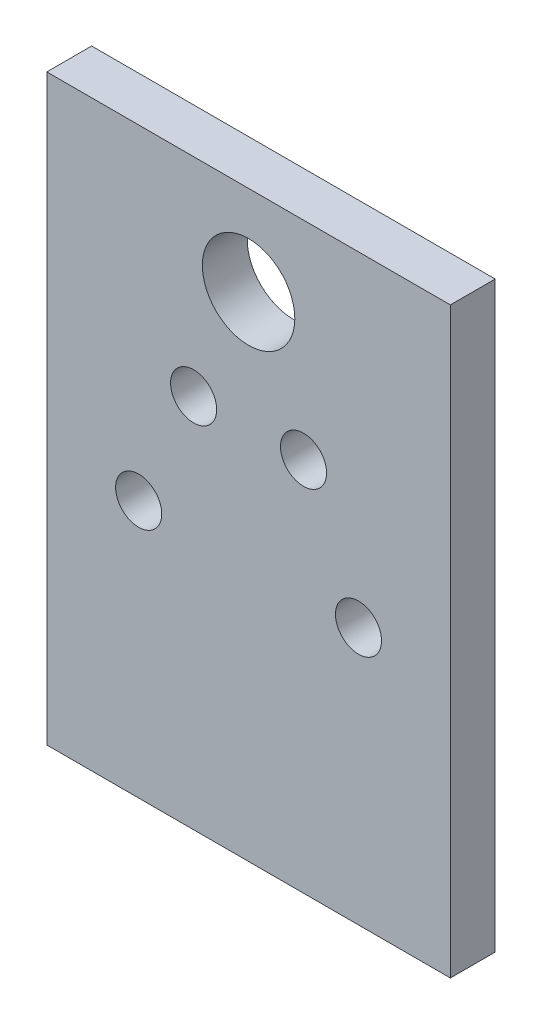
SolidWorks part; units mm, degrees
material "1060 Alloy"
ref_plane "Front Plane" through (0, 0, 0) normal (0, 0, 1) x (1, 0, 0)
ref_plane "Top Plane" through (0, 0, 0) normal (0, 1, 0) x (1, 0, 0)
ref_plane "Right Plane" through (0, 0, 0) normal (1, 0, 0) x (0, 0, -1)
sketch "Sketch1" plane through (0, 0, 0) normal (0, 0, 1) x (1, 0, 0)
  line L0 (0, 12.7) -> (0, 69.85) construction
  line L1 (-28.575, 12.7) -> (28.575, 12.7) construction
  line L2 (-28.575, 12.7) -> (-28.575, -12.7)
  line L3 (-28.575, -12.7) -> (28.575, -12.7)
  line L4 (28.575, 12.7) -> (28.575, -12.7)
  line L5 (0, -12.7) -> (0, 12.7) construction
  line L6 (-28.575, 0) -> (28.575, 0) construction
  line L7 (-28.575, 12.7) -> (28.575, 12.7) construction
  line L8 (-28.575, 12.7) -> (-28.575, 57.15)
  line L9 (-28.575, 57.15) -> (28.575, 57.15) construction
  line L10 (28.575, 12.7) -> (28.575, 57.15)
  line L11 (-28.575, 57.15) -> (28.575, 57.15) construction
  line L12 (-28.575, 57.15) -> (-28.575, 69.85)
  line L13 (-28.575, 69.85) -> (28.575, 69.85)
  line L14 (28.575, 57.15) -> (28.575, 69.85)
  line L15 (0, 57.15) -> (-21.1248, 26.9806) construction
  line L16 (0, 57.15) -> (-15.565, 23.7707) construction
  circle A0 centre (0, 57.15) radius 6.5481
  arc A1 (-21.1248, 26.9806) -> (21.1248, 26.9806) centre (0, 57.15) ccw construction
  arc A2 (-22.9969, 24.307) -> (22.9969, 24.307) centre (0, 57.15) ccw construction
  arc A3 (-19.2527, 29.6543) -> (19.2527, 29.6543) centre (0, 57.15) ccw construction
  arc A4 (-19.2527, 29.6543) -> (-22.9969, 24.307) centre (-21.1248, 26.9806) ccw construction
  arc A5 (22.9969, 24.307) -> (19.2527, 29.6543) centre (21.1248, 26.9806) ccw construction
  arc A6 (-10.5624, 42.0653) -> (10.5624, 42.0653) centre (0, 57.15) ccw construction
  arc A7 (-12.4345, 39.3917) -> (12.4345, 39.3917) centre (0, 57.15) ccw construction
  arc A8 (-8.6903, 44.7389) -> (8.6903, 44.7389) centre (0, 57.15) ccw construction
  arc A9 (-8.6903, 44.7389) -> (-12.4345, 39.3917) centre (-10.5624, 42.0653) ccw construction
  arc A10 (12.4345, 39.3917) -> (8.6903, 44.7389) centre (10.5624, 42.0653) ccw construction
  circle A11 centre (-7.7825, 40.4603) radius 3.2639
  circle A12 centre (-15.565, 23.7707) radius 3.2639
  circle A13 centre (7.7825, 40.4603) radius 3.2639
  circle A14 centre (15.565, 23.7707) radius 3.2639
  point P0 (0, 0)
  point P15 (0, 20.32)
  point P20 (0, 38.735)
  dimension "D5" = 13.0962
  dimension "D1" = 12.7
  dimension "D2" = 57.15
  dimension "D3" = 25.4
  dimension "D4" = 57.15
  dimension "D7" = 6.5278
  dimension "D8" = 7.62
  dimension "D9" = 6.5278
  dimension "D10" = 35
  dimension "D11" = 25
extrude "Boss-Extrude1" add sketch "Sketch1" along normal blind 6.35
